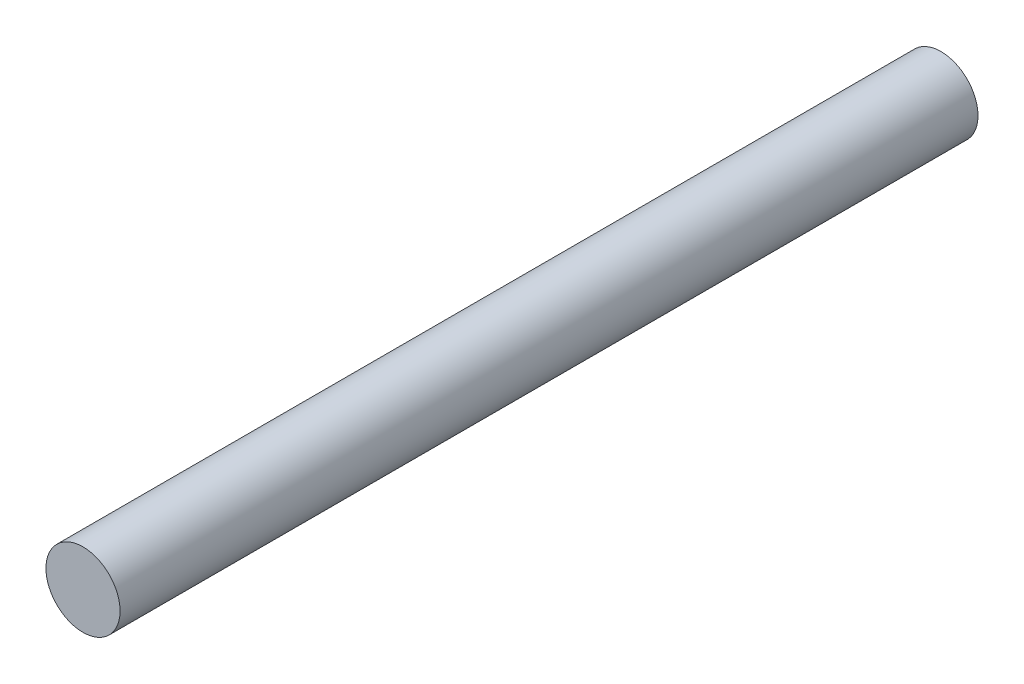
SolidWorks part; units mm, degrees
ref_plane "Plano frontal" through (0, 0, 0) normal (0, 0, 1) x (1, 0, 0)
ref_plane "Plano superior" through (0, 0, 0) normal (0, 1, 0) x (1, 0, 0)
ref_plane "Plano direito" through (0, 0, 0) normal (1, 0, 0) x (0, 0, -1)
sketch "Esboço1" plane through (0, 0, 0) normal (0, 0, 1) x (1, 0, 0)
  circle A0 centre (0, 0) radius 4
  dimension "D1" = 8
extrude "Ressalto-extrusão1" add sketch "Esboço1" along normal mid plane 92.59
